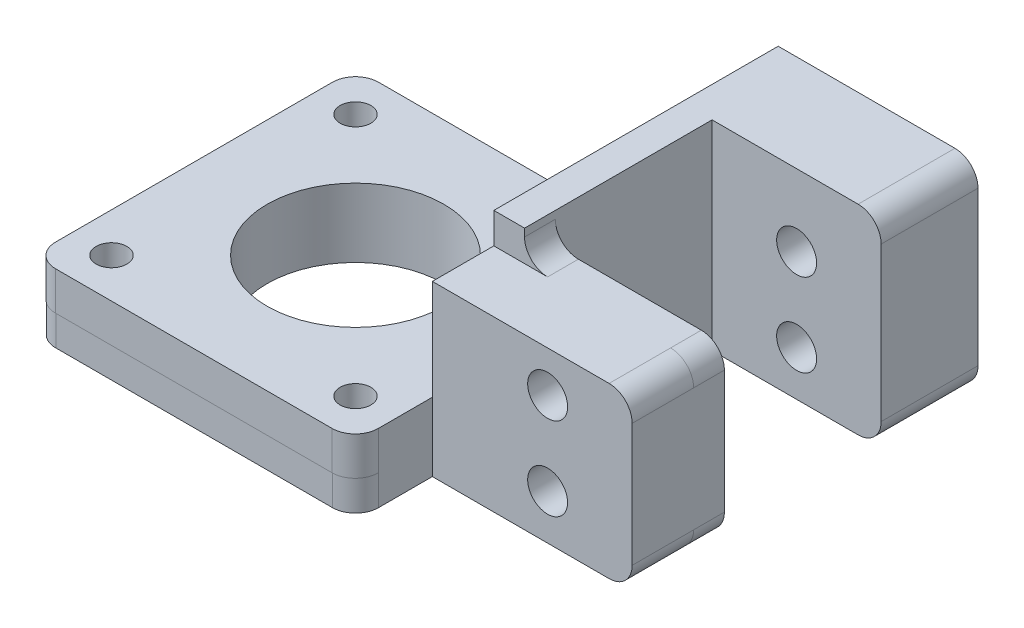
SolidWorks part; units mm, degrees
ref_plane "Front Plane" through (0, 0, 0) normal (0, 0, 1) x (1, 0, 0)
ref_plane "Top Plane" through (0, 0, 0) normal (0, 1, 0) x (1, 0, 0)
ref_plane "Right Plane" through (0, 0, 0) normal (1, 0, 0) x (0, 0, -1)
sketch "Sketch1" plane through (0, 0, 0) normal (0, 0, 1) x (1, 0, 0)
  line L1 (-11, -11) -> (11, -11)
  line L2 (-11, -11) -> (-11, 11)
  line L3 (-11, 11) -> (11, 11)
  line L4 (11, -11) -> (11, 11)
  line L5 (-11, -11) -> (11, 11) construction
  line L6 (-11, 11) -> (11, -11) construction
  point P0 (0, 0)
  dimension "D1" = 22
  dimension "D2" = 22
extrude "Boss-Extrude2" add sketch "Sketch1" along normal blind 4
sketch "Sketch3" plane through (0, 0, 4) normal (0, 0, 1) x (1, 0, 0)
  line L1 (-11, 11) -> (-15, 11)
  line L2 (-11, 11) -> (-11, -11)
  line L3 (-11, -11) -> (-15, -11)
  line L4 (-15, 11) -> (-15, -11)
  dimension "D1" = 4
extrude "Boss-Extrude3" add sketch "Sketch3" against normal blind 24
sketch "Sketch4" plane through (0, 11, 0) normal (0, 1, 0) x (1, 0, 0)
  line L1 (-11, 20) -> (-15, 20)
  line L2 (-11, 20) -> (-11, -4)
  line L3 (-11, -4) -> (-15, -4)
  line L4 (-15, 20) -> (-15, -4)
extrude "Boss-Extrude4" add sketch "Sketch4" along normal blind 4
sketch "Sketch5" plane through (-11, 0, 0) normal (1, 0, 0) x (0, 0, -1)
  line L1 (-4, 11) -> (20, 11)
  line L2 (-4, 11) -> (-4, 15)
  line L3 (-4, 15) -> (20, 15)
  line L4 (20, 11) -> (20, 15)
extrude "Boss-Extrude5" add sketch "Sketch5" against normal blind 24
sketch "Sketch6" plane through (-15, 0, 0) normal (-1, 0, 0) x (0, 0, 1)
  line L1 (-20, -11) -> (22, -11)
  line L2 (-20, -11) -> (-20, -7.0561)
  line L3 (-20, -7.0561) -> (22, -7.0561)
  line L4 (22, -11) -> (22, -7.0561)
  dimension "D1" = 42
extrude "Boss-Extrude6" add sketch "Sketch6" along normal blind 42
sketch "Sketch8" plane through (0, 15, 0) normal (0, 1, 0) x (1, 0, 0)
  line L0 (-11, 20) -> (-35, 20) construction
  line L1 (-57, -22) -> (-15, -22)
  line L2 (-57, -22) -> (-57, 20)
  line L3 (-57, 20) -> (-15, 20)
  line L4 (-15, -22) -> (-15, 20)
  line L5 (-57, 20) -> (-15, 20) construction
extrude "Boss-Extrude7" add sketch "Sketch8" against normal blind 4
sketch "Sketch9" plane through (0, -11, 0) normal (0, -1, 0) x (1, 0, 0)
  circle A0 centre (-36, 1) radius 11.5
  dimension "D1" = 23
extrude "Cut-Extrude1" cut sketch "Sketch9" against normal blind 4
sketch "Sketch10" plane through (0, 15, 0) normal (0, 1, 0) x (1, 0, 0)
  circle A0 centre (-34, -1) radius 2.6
  dimension "D1" = 5.2
extrude "Cut-Extrude2" cut sketch "Sketch10" against normal blind 4
sketch "Sketch11" plane through (0, 0, 4) normal (0, 0, 1) x (1, 0, 0)
  circle A0 centre (0, 5.6604) radius 2.6
  circle A1 centre (0, -5.136) radius 2.6
  dimension "D1" = 5.2
  dimension "D2" = 5.2
extrude "Cut-Extrude3" cut sketch "Sketch11" against normal blind 4
fillet "Fillet1" radius 3 10 edges at (-11, 11, 2) (11, 11, 2) (11, -11, 2) (-15, -9.0281, 22) (-57, -9.0281, 22) (-57, -9.0281, -20) (-57, 13, -20) (-11, 2, -20) (-15, 13, 22) (-57, 13, 22)
sketch "Sketch12" plane through (0, 15, 0) normal (0, 1, 0) x (1, 0, 0)
  line L1 (-40.0637, -6.0537) -> (-28.4493, -6.0537)
  line L2 (-40.0637, -6.0537) -> (-40.0637, 3.8424)
  line L3 (-40.0637, 3.8424) -> (-28.4493, 3.8424)
  line L4 (-28.4493, -6.0537) -> (-28.4493, 3.8424)
extrude "Boss-Extrude8" add sketch "Sketch12" against normal blind 4
sketch "Sketch13" plane through (0, 11, 0) normal (0, -1, 0) x (1, 0, 0)
  circle A0 centre (-36, 1) radius 2.6
  dimension "D1" = 5.2
extrude "Cut-Extrude5" cut sketch "Sketch13" against normal blind 4
sketch "Sketch15" plane through (0, -11, 0) normal (0, -1, 0) x (1, 0, 0)
  line L0 (-36, 1) -> (-20.1255, 16.8745) construction
  line L1 (-36, 1) -> (-51.8745, 16.8745) construction
  line L2 (-36, 1) -> (-51.8745, -14.8745) construction
  line L3 (-36, 1) -> (-20.1255, -14.8745) construction
  circle A0 centre (-20.1255, 16.8745) radius 2
  circle A1 centre (-51.8745, 16.8745) radius 2
  circle A2 centre (-51.8745, -14.8745) radius 2
  circle A3 centre (-20.1255, -14.8745) radius 2
  dimension "D2" = 4
  dimension "D3" = 4
  dimension "D4" = 4
  dimension "D5" = 4
  dimension "D1" = 22.45
extrude "Cut-Extrude7" cut sketch "Sketch15" against normal through all
sketch "Sketch16" plane through (0, 11, 0) normal (0, -1, 0) x (1, 0, 0)
  line L1 (-15, -20) -> (-57, -20)
  line L2 (-15, -20) -> (-15, 22)
  line L3 (-15, 22) -> (-57, 22)
  line L4 (-57, -20) -> (-57, 22)
extrude "Cut-Extrude8" cut sketch "Sketch16" against normal blind 10
sketch "Sketch17" plane through (0, -7.0561, 0) normal (0, 1, 0) x (1, 0, 0)
  line L1 (-57, 20) -> (-15, 20)
  line L2 (-57, 20) -> (-57, -22.0383)
  line L3 (-57, -22.0383) -> (-15, -22.0383)
  line L4 (-15, 20) -> (-15, -22.0383)
extrude "Boss-Extrude9" add sketch "Sketch17" along normal blind 5
fillet "Fillet2" radius 3 1 edges at (-15, -4.5561, 22.0383)
fillet "Fillet3" radius 3 2 edges at (-57, -4.5561, -20) (-57, -4.5561, 22.0383)
sketch "Sketch18" plane through (0, -7.0561, 0) normal (0, -1, 0) x (1, 0, 0)
  circle A0 centre (-20.1255, 16.8745) radius 2
  circle A1 centre (-51.8745, 16.8745) radius 2
  circle A2 centre (-51.8745, -14.8745) radius 2
  circle A3 centre (-20.1255, -14.8745) radius 2
  circle A4 centre (-36, 1) radius 11.5
extrude "Cut-Extrude9" cut sketch "Sketch18" against normal blind 5
sketch "Sketch19" plane through (0, 0, 4) normal (0, 0, 1) x (1, 0, 0)
  line L1 (-15, -11) -> (11, -11)
  line L2 (-15, -11) -> (-15, 11)
  line L3 (-15, 11) -> (11, 11)
  line L4 (11, -11) -> (11, 11)
extrude "Boss-Extrude11" add sketch "Sketch19" along normal blind 8
fillet "Fillet4" radius 3 1 edges at (11, 11, 8)
fillet "Fillet5" radius 3 1 edges at (11, -11, 8)
sketch "Sketch20" plane through (0, 15, 0) normal (0, 1, 0) x (1, 0, 0)
  line L1 (-11, 0) -> (-15, 0)
  line L2 (-11, 0) -> (-11, 20)
  line L3 (-11, 20) -> (-15, 20)
  line L4 (-15, 0) -> (-15, 20)
extrude "Boss-Extrude12" add sketch "Sketch20" against normal through all
sketch "Sketch21" plane through (0, 0, -20) normal (0, 0, -1) x (-1, 0, 0)
  line L1 (11, 15) -> (15, 15)
  line L2 (11, 15) -> (11, -11)
  line L3 (11, -11) -> (15, -11)
  line L4 (15, 15) -> (15, -11)
extrude "Boss-Extrude13" add sketch "Sketch21" along normal blind 13
sketch "Sketch25" plane through (-11, 0, 0) normal (1, 0, 0) x (0, 0, -1)
  line L0 (33, -11) -> (0, -11) construction
  line L1 (33, 15) -> (20.4, 15)
  line L2 (33, 15) -> (33, -11)
  line L3 (33, -11) -> (20.4, -11)
  line L4 (20.4, 15) -> (20.4, -11)
  dimension "D1" = 12.6
extrude "Boss-Extrude15" add sketch "Sketch25" along normal blind 22
fillet "Fillet8" radius 3 1 edges at (11, 15, -26.7)
fillet "Fillet9" radius 3 1 edges at (11, -11, -26.7)
sketch "Sketch27" plane through (0, 0, 0) normal (0, 0, -1) x (-1, 0, 0)
  circle A0 centre (0, 5.6604) radius 2.6
  circle A1 centre (0, -5.136) radius 2.6
extrude "Cut-Extrude10" cut sketch "Sketch27" against normal blind 22
sketch "Sketch28" plane through (0, 0, 12) normal (0, 0, 1) x (1, 0, 0)
  circle A0 centre (0, 5.6604) radius 2.6
  circle A1 centre (0, -5.136) radius 2.6
extrude "Cut-Extrude11" cut sketch "Sketch28" against normal through all
